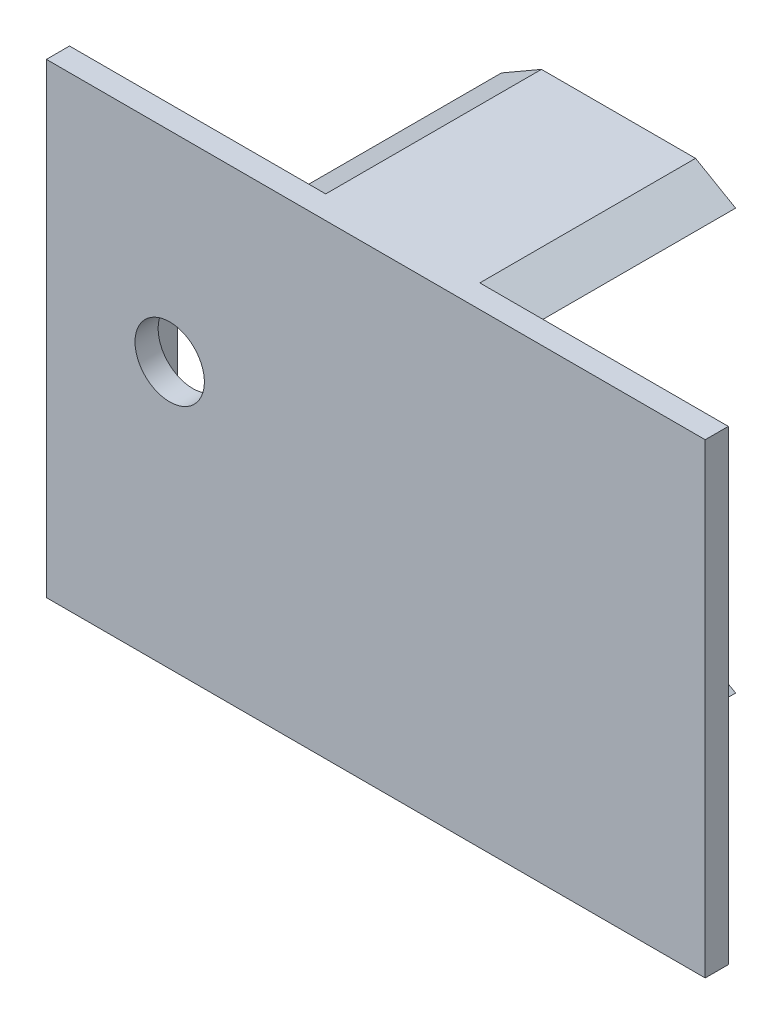
SolidWorks part; units mm, degrees
ref_plane "Front Plane" through (0, 0, 0) normal (0, 0, 1) x (1, 0, 0)
ref_plane "Top Plane" through (0, 0, 0) normal (0, 1, 0) x (1, 0, 0)
ref_plane "Right Plane" through (0, 0, 0) normal (1, 0, 0) x (0, 0, -1)
sketch "Sketch1" plane through (0, 0, 0) normal (0, 0, 1) x (1, 0, 0)
  line L1 (-21.375, -15.125) -> (21.375, -15.125)
  line L2 (-21.375, -15.125) -> (-21.375, 15.125)
  line L3 (-21.375, 15.125) -> (21.375, 15.125)
  line L4 (21.375, -15.125) -> (21.375, 15.125)
  line L5 (-21.375, -15.125) -> (21.375, 15.125) construction
  line L6 (-21.375, 15.125) -> (21.375, -15.125) construction
  point P0 (0, 0)
  dimension "D1" = 42.75
  dimension "D2" = 30.25
extrude "Boss-Extrude1" add sketch "Sketch1" along normal blind 1.5 contours L2 L1 L4 L3
sketch "Sketch2" plane through (0, 0, 0) normal (0, 0, -1) x (-1, 0, 0)
  line L6 (7.3481, -13.625) -> (4.75, -12.125)
  line L7 (4.75, -15.125) -> (7.3481, -13.625)
  line L8 (-5.25, -15.125) -> (4.75, -15.125)
  line L9 (-7.8481, -13.625) -> (-5.25, -15.125)
  line L10 (-5.25, -12.125) -> (-7.8481, -13.625)
  line L11 (4.75, -12.125) -> (-5.25, -12.125)
  line L12 (7.3481, -13.625) -> (4.75, -12.125)
  line L13 (4.75, -15.125) -> (7.3481, -13.625)
  line L14 (-5.25, -15.125) -> (4.75, -15.125)
  line L15 (-7.8481, -13.625) -> (-5.25, -15.125)
  line L16 (-5.25, -12.125) -> (-7.8481, -13.625)
  line L17 (4.75, -12.125) -> (-5.25, -12.125)
  line L18 (-7.8481, 13.625) -> (-5.25, 12.125)
  line L19 (-5.25, 12.125) -> (4.75, 12.125)
  line L20 (4.75, 12.125) -> (7.3481, 13.625)
  line L21 (7.3481, 13.625) -> (4.75, 15.125)
  line L22 (4.75, 15.125) -> (-5.25, 15.125)
  line L23 (-5.25, 15.125) -> (-7.8481, 13.625)
  line L24 (-7.8481, 13.625) -> (-5.25, 12.125)
  line L25 (-5.25, 12.125) -> (4.75, 12.125)
  line L26 (4.75, 12.125) -> (7.3481, 13.625)
  line L27 (7.3481, 13.625) -> (4.75, 15.125)
  line L28 (4.75, 15.125) -> (-5.25, 15.125)
  line L29 (-5.25, 15.125) -> (-7.8481, 13.625)
  line L32 (3.124, 0) -> (-3.124, 0) construction
  point P27 (0, 0)
  dimension "D1" = 0
  dimension "D2" = 0
extrude "Boss-Extrude2" add sketch "Sketch2" along normal up to surface (14 mm away)
sketch "Sketch3" plane through (0, 0, 0) normal (0, 0, -1) x (-1, 0, 0)
  line L0 (21.375, -7.125) -> (19.375, -7.125) construction
  line L1 (19.375, 0.875) -> (21.375, 0.875) construction
  line L2 (21.375, -7.125) -> (19.375, -7.125) construction
  line L3 (19.375, 0.875) -> (21.375, 0.875) construction
  line L5 (19.375, -6.925) -> (21.375, -6.925)
  line L6 (19.375, -6.925) -> (19.375, 0.675)
  line L7 (19.375, 0.675) -> (21.375, 0.675)
  line L8 (21.375, -6.925) -> (21.375, 0.675)
  line L9 (21.375, -15.125) -> (21.375, 15.125) construction
  dimension "D1" = 0.2
  dimension "D2" = 0.2
extrude "Boss-Extrude3" add sketch "Sketch3" along normal offset from surface (5 mm away) 12
sketch "Sketch4" plane through (0, 0, 0) normal (0, 0, -1) x (-1, 0, 0)
  line L0 (21.375, 0.675) -> (21.375, 15.125) construction
  line L1 (21.375, 15.125) -> (4.75, 15.125) construction
  circle A0 centre (13.375, 2.125) radius 2.25
  dimension "D1" = 4.5
  dimension "D2" = 8
  dimension "D3" = 13
extrude "Cut-Extrude1" cut sketch "Sketch4" against normal through all
